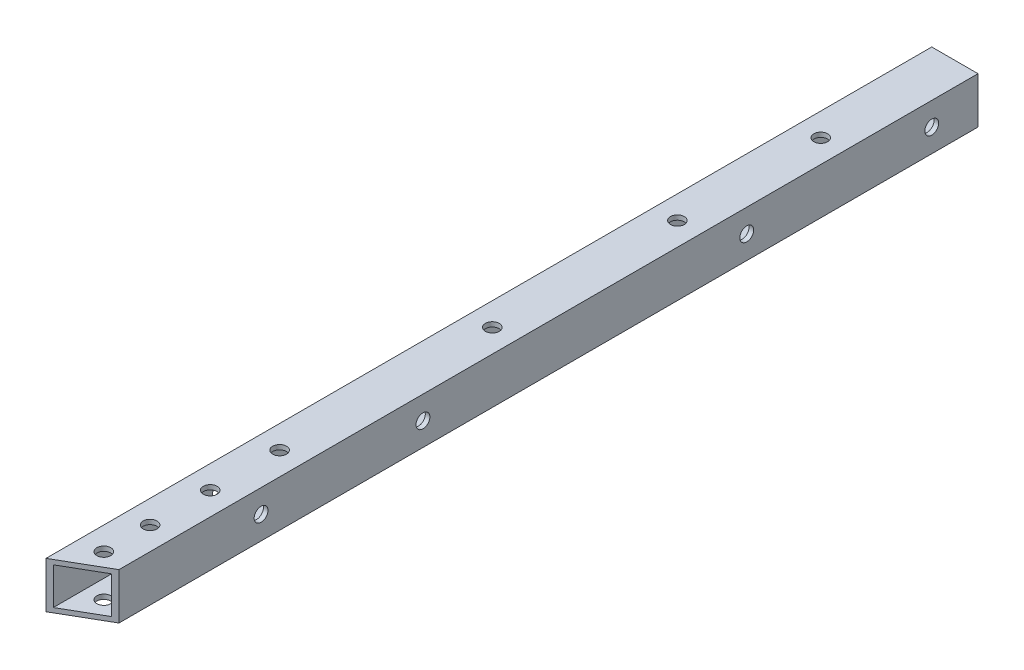
SolidWorks part; units mm, degrees
material "6063-O"
ref_plane "前视基准面" through (0, 0, 0) normal (0, 0, 1) x (1, 0, 0)
ref_plane "上视基准面" through (0, 0, 0) normal (0, 1, 0) x (1, 0, 0)
ref_plane "右视基准面" through (0, 0, 0) normal (1, 0, 0) x (0, 0, -1)
other "Configuration Table"
sketch "草图1" plane through (0, 0, 0) normal (0, 0, 1) x (1, 0, 0)
  line L1 (-5, -5) -> (5, -5)
  line L2 (-5, -5) -> (-5, 5)
  line L3 (-5, 5) -> (5, 5)
  line L4 (5, -5) -> (5, 5)
  line L5 (-5, -5) -> (5, 5) construction
  line L6 (-5, 5) -> (5, -5) construction
  point P4 (0, 0)
  dimension "D1" = 10
  dimension "D2" = 10
extrude "拉伸-薄壁1" add sketch "草图1" along normal blind 191.5 thin thin type one direction reverse wall 1
sketch "草图2" plane through (0, -5, 0) normal (0, -1, 0) x (1, 0, 0)
  line L0 (0, 191.5) -> (0, 183.9944) construction
  line L1 (-5, 191.5) -> (5, 191.5) construction
  line L2 (0, 0) -> (0, 29) construction
  line L3 (-5, 0) -> (5, 0) construction
  line L4 (-5, 191.5) -> (5, 185.7265)
  line L5 (-5, 191.5) -> (-5, 0) construction
  line L6 (5, 191.5) -> (5, 0) construction
  line L7 (5, 185.7265) -> (5, 191.5)
  line L8 (5, 191.5) -> (-5, 191.5)
  line L9 (0, 29) -> (0, 183.9944) construction
  circle A0 centre (0, 183.9944) radius 1.5
  circle A1 centre (0, 29) radius 1.5
  circle A2 centre (0, 173.9944) radius 1.5
  circle A3 centre (0, 100) radius 1.5
  circle A4 centre (0, 60) radius 1.5
  circle A5 centre (0, 146) radius 1.5
  circle A6 centre (0, 161) radius 1.5
  dimension "D1" = 3
  dimension "D3" = 3
  dimension "D6" = 10
  dimension "D7" = 60
  dimension "D8" = 40
  dimension "D2" = 4
  dimension "D9" = 46
  dimension "D10" = 15
  dimension "D4" = 29
  dimension "D5" = 30
extrude "切除-拉伸1" cut sketch "草图2" against normal through all
sketch "草图3" plane through (-5, 0, 0) normal (-1, 0, 0) x (0, 0, 1)
  line L0 (0, 0) -> (220, 0) construction
  line L1 (0, 5) -> (0, -5) construction
  circle A0 centre (50, 0) radius 1.5
  circle A1 centre (79.7, 0) radius 1.5 construction
  circle A2 centre (120, 0) radius 1.5
  circle A3 centre (10, 0) radius 1.5
  circle A4 centre (155, 0) radius 1.5
  dimension "D1" = 3
  dimension "D2" = 50
  dimension "D3" = 29.7
  dimension "D4" = 70
  dimension "D5" = 10
  dimension "D6" = 35
extrude "切除-拉伸2" cut sketch "草图3" against normal through all
